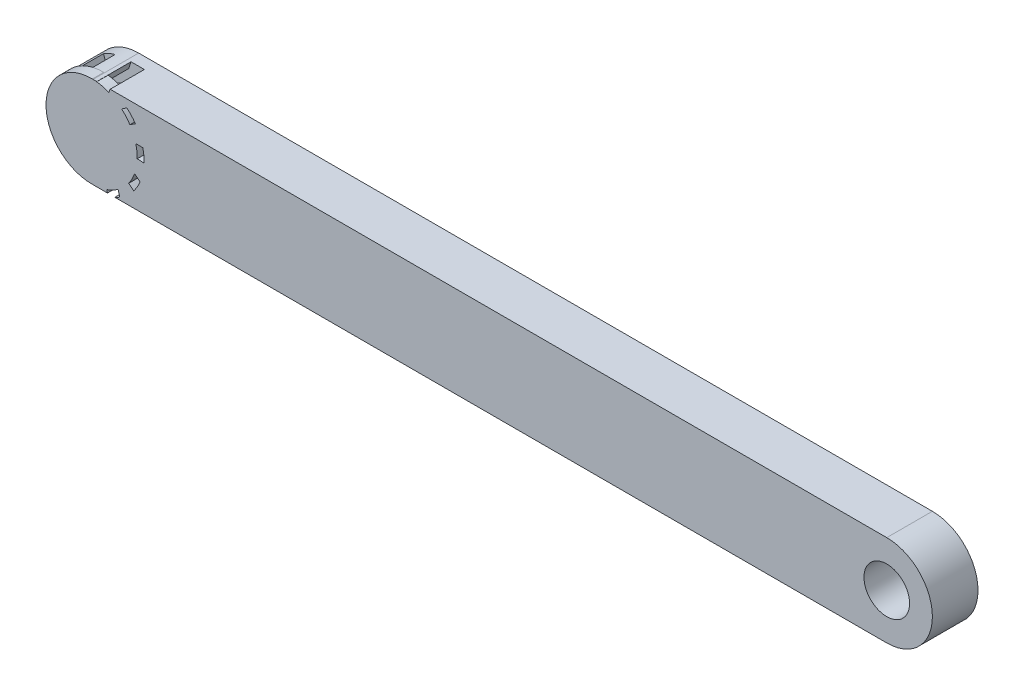
SolidWorks part; units mm, degrees
material "1060 Alloy"
ref_plane "Front Plane" through (0, 0, 0) normal (0, 0, 1) x (1, 0, 0)
ref_plane "Top Plane" through (0, 0, 0) normal (0, 1, 0) x (1, 0, 0)
ref_plane "Right Plane" through (0, 0, 0) normal (1, 0, 0) x (0, 0, -1)
sketch "Sketch1" plane through (0, 0, 0) normal (0, 0, 1) x (1, 0, 0)
  line L0 (-71.3706, 0) -> (276.6294, 0) construction
  line L1 (-71.3706, 20) -> (276.6294, 20)
  line L2 (-71.3706, -20) -> (276.6294, -20)
  arc A0 (-71.3706, 20) -> (-71.3706, -20) centre (-71.3706, 0) ccw
  arc A1 (276.6294, -20) -> (276.6294, 20) centre (276.6294, 0) ccw
  circle A2 centre (-71.3706, 0) radius 10
  circle A3 centre (276.6294, 0) radius 10
  point P3 (102.6294, 0)
extrude "Boss-Extrude1" add sketch "Sketch1" along normal blind 20
sketch "Sketch2" plane through (0, 0, 0) normal (0, 0, -1) x (-1, 0, 0)
  line L0 (71.3706, -20) -> (71.3706, -25)
  line L1 (62.5643, -17.9569) -> (58.8706, -21.6506)
  arc A0 (62.5643, -17.9569) -> (71.3706, -20) centre (71.3706, 0) ccw
  arc A1 (58.8706, -21.6506) -> (71.3706, -25) centre (71.3706, 0) ccw
  arc A2 (71.3706, -20) -> (71.3706, 20) centre (71.3706, 0) ccw construction
  dimension "D1" = 50
  dimension "D2" = 45
extrude "Boss-Extrude2" add sketch "Sketch2" along normal blind 20
ref_plane "Plane1" through (0, 0, 15) normal (0, 0, 1) x (1, 0, 0)
sketch "Sketch5" plane through (0, 0, 15) normal (0, 0, 1) x (1, 0, 0)
  circle A0 centre (-72.0022, 0) radius 20
  arc A1 (-71.3706, 20) -> (-71.3706, -20) centre (-71.3706, 0) ccw construction
  circle A2 centre (-72.0022, 0) radius 13.4404
sketch "Sketch6" plane through (0, 0, 20) normal (0, 0, 1) x (1, 0, 0)
  arc A0 (-88.394, 13.4275) -> (-84.4109, 10.3957) centre (-59.492, 47.2654) ccw
  arc A1 (-88.394, 13.4275) -> (-91.2105, 8.6139) centre (-70.967, 0) ccw
  arc A2 (-87.2195, -4.9662) -> (-85.0083, -9.5735) centre (-70.967, 0) ccw
  arc A3 (-91.2105, 8.6139) -> (-87.0346, 5.5353) centre (-59.492, 47.2654) ccw
  arc A4 (-92.9583, 0.6198) -> (-92.4075, -4.93) centre (-70.967, 0) ccw
  arc A5 (-92.4075, -4.93) -> (-87.2195, -4.9662) centre (-89.4654, 44.9833) ccw
  arc A6 (-92.9583, 0.6198) -> (-87.9538, 0.5082) centre (-89.4654, 44.9833) ccw
  arc A7 (-77.1732, 21.1065) -> (-75.7329, 16.3124) centre (-33.9016, 31.4937) ccw
  arc A8 (-77.1732, 21.1065) -> (-82.2812, 18.8677) centre (-70.967, 0) ccw
  arc A9 (-82.2812, 18.8677) -> (-80.7124, 13.9225) centre (-33.9016, 31.4937) ccw
  arc A10 (-63.5819, 20.7234) -> (-65.2345, 15.9983) centre (-22.469, 3.6924) ccw
  arc A11 (-63.5819, 20.7234) -> (-69.0302, 21.9146) centre (-70.967, 0) ccw
  arc A12 (-69.0302, 21.9146) -> (-70.6678, 16.9917) centre (-22.469, 3.6924) ccw
  arc A13 (-52.8114, 12.4247) -> (-56.9257, 9.5735) centre (-29.5609, -25.5192) ccw
  arc A14 (-52.8114, 12.4247) -> (-56.5191, 16.5909) centre (-70.967, 0) ccw
  arc A15 (-56.5191, 16.5909) -> (-60.7375, 13.5707) centre (-29.5609, -25.5192) ccw
  arc A16 (-48.9757, -0.6198) -> (-53.9802, -0.5082) centre (-52.4686, -44.9833) ccw
  arc A17 (-48.9757, -0.6198) -> (-49.5265, 4.93) centre (-70.967, 0) ccw
  arc A18 (-49.5265, 4.93) -> (-54.7144, 4.9662) centre (-52.4686, -44.9833) ccw
  arc A19 (-53.54, -13.4275) -> (-57.5231, -10.3957) centre (-82.442, -47.2654) ccw
  arc A20 (-53.54, -13.4275) -> (-50.7235, -8.6139) centre (-70.967, 0) ccw
  arc A21 (-50.7235, -8.6139) -> (-54.8994, -5.5353) centre (-82.442, -47.2654) ccw
  arc A22 (-64.7607, -21.1065) -> (-66.2011, -16.3124) centre (-108.0324, -31.4937) ccw
  arc A23 (-64.7607, -21.1065) -> (-59.6528, -18.8677) centre (-70.967, 0) ccw
  arc A24 (-59.6528, -18.8677) -> (-61.2216, -13.9225) centre (-108.0324, -31.4937) ccw
  arc A25 (-78.3521, -20.7234) -> (-76.6995, -15.9983) centre (-119.465, -3.6924) ccw
  arc A26 (-78.3521, -20.7234) -> (-72.9037, -21.9146) centre (-70.967, 0) ccw
  arc A27 (-72.9037, -21.9146) -> (-71.2662, -16.9917) centre (-119.465, -3.6924) ccw
  arc A28 (-89.1226, -12.4247) -> (-85.0083, -9.5735) centre (-112.3731, 25.5192) ccw
  arc A29 (-89.1226, -12.4247) -> (-85.4149, -16.5909) centre (-70.967, 0) ccw
  arc A30 (-85.4149, -16.5909) -> (-81.1965, -13.5707) centre (-112.3731, 25.5192) ccw
  arc A31 (-71.2662, -16.9917) -> (-66.2011, -16.3124) centre (-70.967, 0) ccw
  arc A32 (-61.2216, -13.9225) -> (-57.5231, -10.3957) centre (-70.967, 0) ccw
  arc A33 (-54.8994, -5.5353) -> (-53.9802, -0.5082) centre (-70.967, 0) ccw
  arc A34 (-54.7144, 4.9662) -> (-56.9257, 9.5735) centre (-70.967, 0) ccw
  arc A35 (-87.0346, 5.5353) -> (-87.9538, 0.5082) centre (-70.967, 0) ccw
  arc A36 (-80.7124, 13.9225) -> (-84.4109, 10.3957) centre (-70.967, 0) ccw
  arc A37 (-70.6678, 16.9917) -> (-75.7329, 16.3124) centre (-70.967, 0) ccw
  arc A38 (-60.7375, 13.5707) -> (-65.2345, 15.9983) centre (-70.967, 0) ccw
  arc A39 (-81.1965, -13.5707) -> (-76.6995, -15.9983) centre (-70.967, 0) ccw
  circle A40 centre (-57.8403, 49.4636) radius 47.2504
  point P54 (-70.967, 0)
  dimension "D1" = 10
extrude "Cut-Extrude1" cut sketch "Sketch6" against normal blind 15 contours A39 A25 A26 A27 A31 A22 A23 A24 A32 A19 A20 A21 A33 A16 A17 A18 A34 A13 A14 A15 A38 A10 A11 A12 A37 A7 A8 A9 A36 A0 A1 A3 A35 A6 A4 A5 A2 A28 A29 A30
extrude "Boss-Extrude3" add sketch "Sketch5" along normal blind 5 contours A0
